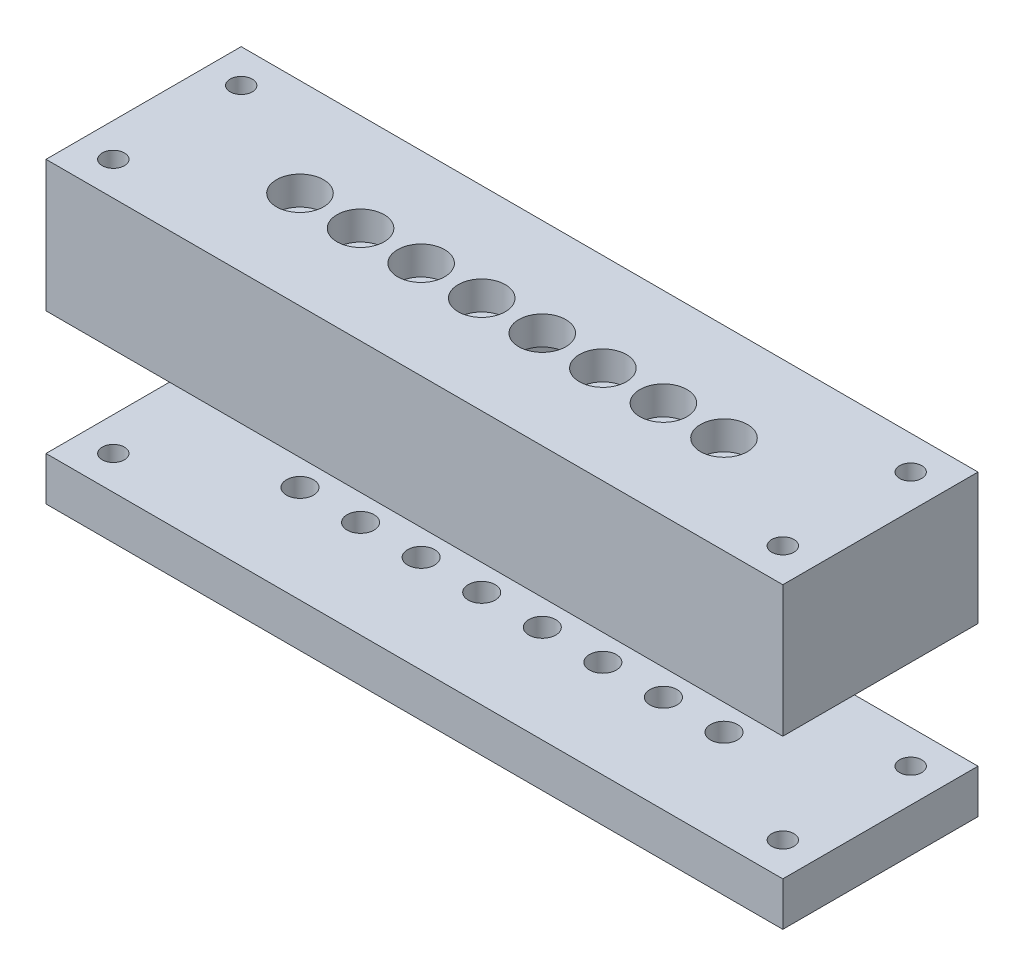
SolidWorks part; units mm, degrees
ref_plane "Front Plane" through (0, 0, 0) normal (0, 0, 1) x (1, 0, 0)
ref_plane "Top Plane" through (0, 0, 0) normal (0, 1, 0) x (1, 0, 0)
ref_plane "Right Plane" through (0, 0, 0) normal (1, 0, 0) x (0, 0, -1)
sketch "Sketch1" plane through (0, 0, 0) normal (0, 0, 1) x (1, 0, 0)
  line L0 (-31.5, 22.175) -> (-31.5, -22.175) construction
  line L1 (54.74, -22.175) -> (-54.74, -22.175)
  line L2 (54.74, -22.175) -> (54.74, 22.175)
  line L3 (54.74, 22.175) -> (-54.74, 22.175)
  line L4 (-54.74, -22.175) -> (-54.74, 22.175)
  line L5 (54.74, -22.175) -> (-54.74, 22.175) construction
  line L6 (54.74, 22.175) -> (-54.74, -22.175) construction
  line L7 (-34.225, -22.175) -> (-34.225, -20.675)
  line L8 (-34.225, -20.675) -> (-33.5, -20.675)
  line L9 (-33.5, -20.675) -> (-33.5, -17.675)
  line L10 (-33.5, -17.675) -> (-33.5, -15.675)
  line L11 (-33.5, -15.675) -> (-33.5, 2.675)
  line L12 (-33.5, 2.675) -> (-33.5, 4.675)
  line L13 (-33.5, -15.675) -> (-31.5, -15.675) construction
  line L14 (-33.5, 4.675) -> (-34.5, 4.675)
  line L15 (-34.5, 4.675) -> (-34.5, 9.675)
  line L16 (-34.5, 9.675) -> (-35, 9.675)
  line L17 (-35, 9.675) -> (-35, 22.175)
  line L18 (-33.5, 4.675) -> (-31.5, 4.675) construction
  line L19 (-35, 13.925) -> (-31.5, 13.925) construction
  line L20 (-35, 17.925) -> (-31.5, 17.925) construction
  line L21 (-33.25, 17.925) -> (-33.25, 13.925) construction
  line L22 (-33.5, 2.675) -> (-31.5, 2.675) construction
  point P0 (0, 0)
  point P10 (-31.5, -19.175)
  point P13 (-33.5, -19.175)
  point P20 (-31.5, 7.175)
  point P24 (-34.5, 7.175)
  point P31 (-33.25, 15.925)
  point P32 (-35, 15.925)
  dimension "D1" = 109.48
  dimension "D2" = 3
  dimension "D4" = 23.24
  dimension "D3" = 3
  dimension "D5" = 5.45
  dimension "D6" = 4
  dimension "D7" = 2
  dimension "D8" = 18.35
  dimension "D9" = 2
  dimension "D10" = 5
  dimension "D11" = 15
  dimension "D12" = 6
  dimension "D13" = 7
  dimension "D14" = 4
extrude "Boss-Extrude1" add sketch "Sketch1" along normal mid plane 29 contours L16 L17 L3 L4 L1 L7 L8 L9 L10 L11 L12 L14 L15 | L17 L16 L15 L14 L12 L11 L10 L9 L8 L7 L1 L2 L3
sketch "Sketch3" plane through (0, 0, 0) normal (0, 0, 1) x (1, 0, 0)
  line L0 (-34.225, -22.175) -> (-34.225, -20.675) construction
  line L1 (-34.225, -20.675) -> (-33.5, -20.675) construction
  line L2 (-33.5, -20.675) -> (-33.5, -17.675) construction
  line L3 (-33.5, -15.675) -> (-31.5, -15.675) construction
  line L4 (-33.5, -17.675) -> (-33.5, -15.675) construction
  line L5 (-35, 17.925) -> (-31.5, 17.925) construction
  line L6 (-33.25, 17.925) -> (-33.25, 13.925) construction
  line L7 (-35, 13.925) -> (-31.5, 13.925) construction
  line L9 (-31.5, 22.175) -> (-31.5, -22.175) construction
  line L10 (-33.5, -15.675) -> (-33.5, 2.675) construction
  line L11 (-33.5, 2.675) -> (-33.5, 4.675) construction
  line L12 (-33.5, 4.675) -> (-34.5, 4.675) construction
  line L13 (-34.5, 4.675) -> (-34.5, 9.675) construction
  line L14 (-34.5, 9.675) -> (-35, 9.675) construction
  line L15 (-35, 9.675) -> (-35, 22.175) construction
  line L16 (-34.225, -22.175) -> (-34.225, -20.675)
  line L17 (-34.225, -20.675) -> (-33.5, -20.675)
  line L18 (-33.5, -20.675) -> (-33.5, -17.675)
  line L19 (-33.5, -15.675) -> (-31.5, -15.675) construction
  line L20 (-33.5, -17.675) -> (-33.5, -15.675)
  line L21 (-35, 17.925) -> (-31.5, 17.925) construction
  line L22 (-33.25, 17.925) -> (-33.25, 13.925) construction
  line L23 (-35, 13.925) -> (-31.5, 13.925) construction
  line L25 (-31.5, 22.175) -> (-31.5, -22.175)
  line L26 (-33.5, -15.675) -> (-33.5, 2.675)
  line L27 (-33.5, 2.675) -> (-33.5, 4.675)
  line L28 (-33.5, 4.675) -> (-34.5, 4.675)
  line L29 (-34.5, 4.675) -> (-34.5, 9.675)
  line L30 (-34.5, 9.675) -> (-35, 9.675)
  line L31 (-35, 9.675) -> (-35, 22.175)
  line L32 (-34.225, -22.175) -> (-31.5, -22.175)
  line L33 (-35, 22.175) -> (-31.5, 22.175)
  point P0 (-31.5, 7.175)
  point P2 (-31.5, -19.175)
revolve "Cut-Revolve1" cut sketch "Sketch3" angle 360 about L25
pattern_linear "LPattern1" count 8 spacing 9 along (1, 0, 0) of "Cut-Revolve1"
sketch "Sketch4" plane through (0, 0, 0) normal (0, 0, 1) x (1, 0, 0)
  line L0 (-35, 13.925) -> (-31.5, 13.925) construction
  line L1 (-35, 17.925) -> (-31.5, 17.925) construction
  line L2 (-35, 13.925) -> (-31.5, 13.925) construction
  line L3 (-35, 17.925) -> (-31.5, 17.925) construction
  line L4 (-0.75, 17.925) -> (0.75, 17.925) construction
  line L5 (-42.75, 17.925) -> (-0.75, 17.925)
  line L6 (-42.75, 17.925) -> (-42.75, 13.925)
  line L7 (-42.75, 13.925) -> (-0.75, 13.925)
  line L8 (42.75, 17.925) -> (42.75, 13.925)
  line L9 (0.75, 17.925) -> (42.75, 17.925)
  line L10 (0.75, 13.925) -> (42.75, 13.925)
  line L11 (-0.75, 13.925) -> (0.75, 13.925) construction
  line L12 (-0.75, 17.925) -> (-0.75, 13.925)
  line L13 (0.75, 17.925) -> (0.75, 13.925)
  point P8 (0, 13.925)
  dimension "D1" = 1.5
  dimension "D2" = 42
extrude "Cut-Extrude1" cut sketch "Sketch4" along normal blind 25 from surface
sketch "Sketch5" plane through (0, 0, 0) normal (0, 0, 1) x (1, 0, 0)
  line L0 (-33.5, -15.675) -> (-31.5, -15.675) construction
  line L2 (-33.5, -15.675) -> (-31.5, -15.675) construction
  line L3 (-33.5, 2.675) -> (-31.5, 2.675) construction
  line L4 (54.74, -22.175) -> (54.74, 22.175) construction
  line L5 (-54.74, -22.175) -> (-54.74, 22.175) construction
  line L6 (54.74, -22.175) -> (54.74, 22.175) construction
  line L7 (-54.74, -22.175) -> (-54.74, 22.175) construction
  line L8 (-33.5, 2.675) -> (-31.5, 2.675) construction
  line L9 (-54.74, 2.675) -> (54.74, 2.675)
  line L10 (-54.74, 2.675) -> (-54.74, -15.675)
  line L11 (-54.74, -15.675) -> (54.74, -15.675)
  line L12 (54.74, 2.675) -> (54.74, -15.675)
  line L13 (-33.5, 2.675) -> (-31.5, 2.675) construction
extrude "Cut-Extrude2" cut sketch "Sketch5" along normal through all from surface at -14.5 starting at face at (21.75, 15.925, -14.5)
sketch "Sketch6" plane through (0, 22.175, 0) normal (0, 1, 0) x (1, 0, 0)
  line L0 (54.74, 14.5) -> (-54.74, 14.5) construction
  line L1 (-54.74, -14.5) -> (-54.74, 14.5) construction
  line L2 (0, -15.95) -> (0, 15.95) construction
  line L3 (-24.3925, 0) -> (24.3925, 0) construction
  circle A0 centre (-49.74, 9.5) radius 1.65
  circle A1 centre (49.74, 9.5) radius 1.65
  circle A2 centre (49.74, -9.5) radius 1.65
  circle A3 centre (-49.74, -9.5) radius 1.65
  dimension "D1" = 3.3
  dimension "D2" = 5
  dimension "D3" = 5
extrude "Cut-Extrude3" cut sketch "Sketch6" against normal through all both and the other way through all
other "Save Bodies1"
equation "\"Plate_height\"= 14.35mm'end to end plate height"
equation "\"Plate_width\"= 85.48mm'end to end plate width"
equation "\"Plate_length\"= 127.76mm'end to end plate length"
equation "\"hole_offset_length_side\"= 11.24mm'offset between well and length side "
equation "\"well2well_distance\"= 9mm'center to center/edge to edge separation between 2 wells"
equation "\"well_diameter\"= 7mm'well diameter"
equation "\"lensL_diameter\"= 3mm'lens diameter on LED side"
equation "\"lensL_height\"= 2mm'lens height on LED side"
equation "\"lensL_focal\"= 3mm'lens focal length on LED side"
equation "\"lensP_diameter\"= 5mm'lens diameter on photodiode side"
equation "\"lensP_height\"= 4mm'lens height on photodiode side"
equation "\"lensP_focal\"= 15mm'lens focal length on photodiode side"
equation "\"filter_length\"= 40mm'filter length"
equation "\"filter_width\"= 25mm'filter width"
equation "\"filter_thickness\"= 2mm'filter thickness"
equation "\"filter2filter_clearance\"= 1.5mm'wall thickness between both filters"
equation "\"LED_diameter\"= 3.45mm'bounding diameter of LED"
equation "\"photodiode_diameter\"= 2.9 * 2mm'bounding diameter of photodiode with optical center aligned with diameter center. Dont forget to align the pcb photodiode with the optical center of your system"
equation "\"D1@Sketch1\"=\"Plate_width\"+2*2+10*2"
equation "\"D2@Sketch1\"=\"lensL_focal\""
equation "\"D4@Sketch1\"=10+2+ \"hole_offset_length_side\""
equation "\"D3@Sketch1\"=\"lensL_height\"+0.5*2"
equation "\"D5@Sketch1\"=\"LED_diameter\"+1*2"
equation "\"D6@Sketch1\"=\"lensL_diameter\"+2*0.5"
equation "\"D8@Sketch1\"=\"Plate_height\"+2*2"
equation "\"D10@Sketch1\"=\"lensP_height\"+0.5*2"
equation "\"D11@Sketch1\"=\"lensP_focal\""
equation "\"D12@Sketch1\"=\"lensP_diameter\"+0.5*2"
equation "\"D13@Sketch1\"=\"photodiode_diameter\"+0.6*2"
equation "\"D1@Boss-Extrude1\"=\"well2well_distance\"+10*2"
equation "\"D14@Sketch1\"=\"filter_thickness\"+1*2"
equation "\"D3@LPattern1\"=\"well2well_distance\""
equation "\"D1@Sketch4\"=\"filter2filter_clearance\""
equation "\"D2@Sketch4\"=\"filter_length\"+1*2"
equation "\"D1@Cut-Extrude1\"=\"filter_width\""
